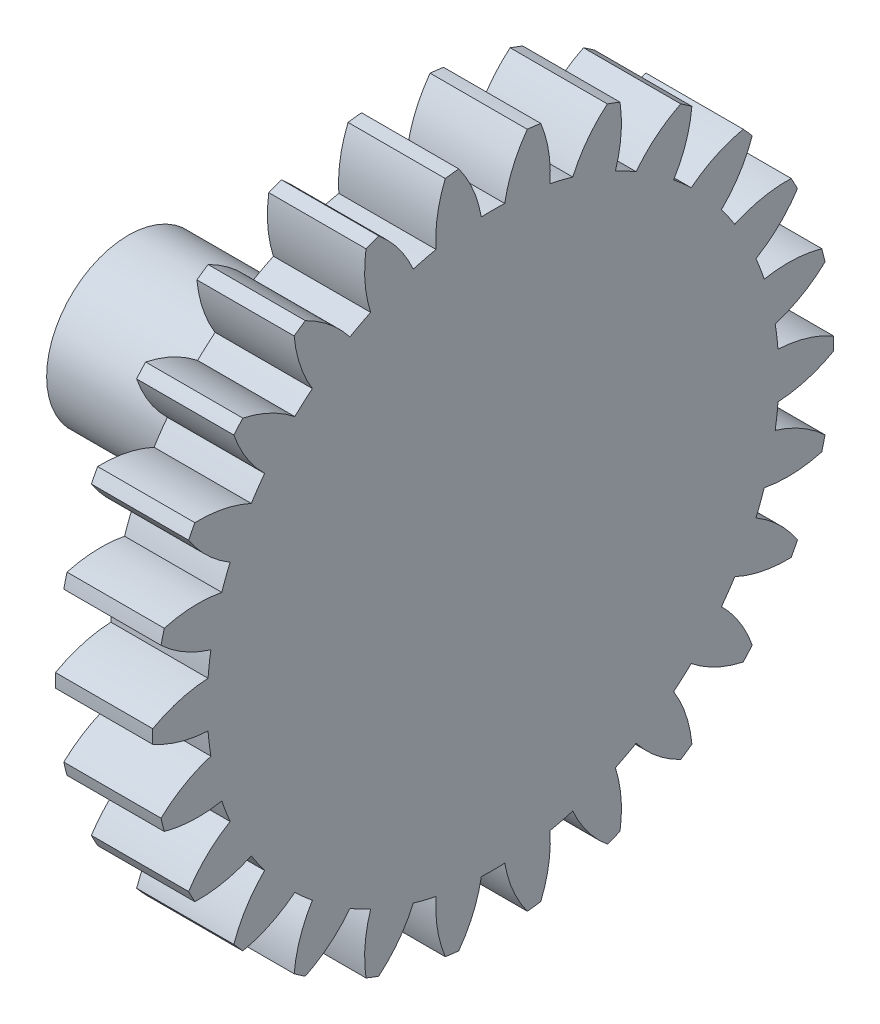
SolidWorks part; units mm, degrees
ref_plane "Plane1" through (0, 0, 0) normal (0, 0, 1) x (1, 0, 0)
ref_plane "Plane2" through (0, 0, 0) normal (0, 1, 0) x (1, 0, 0)
ref_plane "Plane3" through (0, 0, 0) normal (1, 0, 0) x (0, 0, -1)
sketch "HoldingSke" plane through (0, 0, 0) normal (0, 1, 0) x (1, 0, 0)
  line L0 (0, 0) -> (456.5874, -222.6925)
  line L1 (-15, 0) -> (100, 0) construction
  line L2 (0, 0) -> (-2.1039, 2.3779)
  line L3 (0, 0) -> (-11.863, 4.5341)
  line L4 (0, 0) -> (7.762, 3.7858)
  line L5 (0, 0) -> (-47.5972, -17.7524)
  line L6 (0, 0) -> (-4.2111, -2.8413)
  line L7 (-2.1039, 2.3779) -> (8.8308, 51.9871)
  line L8 (-76.2, 54.61) -> (-74.168, 54.61)
  line L9 (-71.009, 38.7566) -> (-53.1078, 45.2721)
  line L10 (-76.2, 71.12) -> (104.1128, 71.12)
  line L11 (0, 0) -> (-5.08, 0)
  line L12 (-76.2, 101.6) -> (-76.1492, 101.6)
  line L13 (24.9733, 27.94) -> (52.9518, 28.4284)
  line L14 (24.9733, 27.94) -> (25.0241, 27.9398)
  line L15 (24.9733, 27.94) -> (100.4021, 29.52)
  circle A0 centre (0, 0) radius 0.9995
  circle A1 centre (0, 0) radius 14.9352
  circle A2 centre (0, 0) radius 38.1
  circle A3 centre (0, 0) radius 0.9995
  dimension "MHD" = 29.8704
  dimension "Hub_dia" = 76.2
  dimension "Bore" = 1.999
  dimension "MBD" = 1.999
  dimension "Num_teeth" = 26
  dimension "Pitch" = 508
  dimension "Overall_len" = 50.8
  dimension "Show_teeth" = 26
  dimension "Thickness" = 5.08
  dimension "OAL" = 50.8001
  dimension "T_dim" = 2.032
  dimension "Ap" = 20
  dimension "H" = 19.05
  dimension "Pitch_radius" = 180.3128
  dimension "Width" = 5.08
  dimension "Backlash" = 0.0508
  dimension "Addendum_fac" = 1
  dimension "Dedendum_fac" = 1.2
  dimension "Clearance_fac" = 0.2
  dimension "Dedendum_add" = 0.0508
sketch "BasProSke" plane through (0, 0, 0) normal (0, 1, 0) x (1, 0, 0)
  line L0 (-10, 0) -> (60, 0) construction
  line L1 (0, 0) -> (0, 17.78)
  line L2 (0, 0) -> (5.08, 0)
  line L3 (5.08, 0) -> (5.08, 17.78)
  line L4 (5.08, 17.78) -> (0, 17.78)
  dimension "Thickness" = 5.08
  dimension "Diameter" = 35.56
revolve "Base-Revolve" add sketch "BasProSke" angle 360 about L0
sketch "TooCutSke" plane through (0, 0, 0) normal (1, 0, 0) x (0, 0, -1)
  line L1 (0, 0) -> (0, 107) construction
  line L2 (0, 0) -> (-1.0857, 16.4743) construction
  line L3 (0, 0) -> (-3.9741, 32.7296) construction
  line L4 (-1.0857, 16.4743) -> (-1.987, 16.3648) construction
  arc A0 (0.6122, 14.9226) -> (-0.6122, 14.9226) centre (0, 0) ccw
  arc A1 (1.8087, 17.7133) -> (-1.8087, 17.7133) centre (0, 0) ccw
  circle A2 centre (0, 0) radius 16.51 construction
  circle A3 centre (0, 0) radius 15.5143 construction
  arc A4 (-0.6122, 14.9226) -> (-1.8087, 17.7133) centre (-7.1175, 13.7853) ccw
  arc A5 (1.8087, 17.7133) -> (0.6122, 14.9226) centre (7.1175, 13.7853) ccw
  dimension "Root_dia" = 29.8704
  dimension "Overcut_dia" = 35.6108
  dimension "Pitch_dia" = 33.02
  dimension "Base_dia" = 31.0287
  dimension "Flank_rad" = 6.604
  dimension "Half_ang" = 6.923
  dimension "Half_CT" = 0.9079
extrude "ToothCut" cut sketch "TooCutSke" along normal through all
fillet "Breaks" [suppressed] radius 0.0254
fillet "RootFillets" [suppressed] radius 0.3048
pattern_circular "TeethCuts" count 26 every 13.846 about axis through (-10, 0, 0) along (1, 0, 0) of "ToothCut", "RootFillets", "Breaks"
sketch "HubNeaOneSke" plane through (0, 0, 0) normal (-1, 0, 0) x (0, 0, 1)
  circle A0 centre (0, 0) radius 14.9352
  dimension "Diameter" = 29.8704
extrude "HubNearOne" [suppressed] add sketch "HubNeaOneSke" along normal blind 45.7201
sketch "HubNeaBotSke" plane through (0, 0, 0) normal (-1, 0, 0) x (0, 0, 1)
  circle A0 centre (0, 0) radius 14.9352
  dimension "Diameter" = 29.8704
extrude "HubNearBoth" [suppressed] add sketch "HubNeaBotSke" along normal blind 22.86
ref_plane "FarPln" through (5.08, 0, 0) normal (1, 0, 0) x (0, 0, -1)
sketch "HubFarSke" plane through (5.08, 0, 0) normal (1, 0, 0) x (0, 0, -1)
  circle A0 centre (0, 0) radius 14.9352
  dimension "Diameter" = 29.8704
extrude "HubFar" [suppressed] add sketch "HubFarSke" along normal blind 22.86
sketch "BorSke" plane through (0, 0, 0) normal (1, 0, 0) x (0, 0, -1)
  circle A0 centre (0, 0) radius 0.9995
  dimension "Diameter" = 1.999
extrude "Bore" cut sketch "BorSke" along normal mid plane 101.6001
sketch "KeySke" plane through (0, 0, 0) normal (1, 0, 0) x (0, 0, -1)
  line L0 (-0.127, 0) -> (-0.127, 1.0325)
  line L1 (-0.127, 1.0325) -> (0.127, 1.0325)
  line L2 (0.127, 1.0325) -> (0.127, 0)
  line L3 (0, 0) -> (0, 34) construction
  line L4 (-0.127, 0) -> (0.127, 0)
  dimension "Offset" = 1.0325
  dimension "Width" = 0.254
extrude "Keyway" [suppressed] cut sketch "KeySke" along normal mid plane 101.6001
pattern_circular "Keyway2" [suppressed] count 2 every 90 about axis through (-10, 0, 0) along (1, 0, 0)
sketch "Sketch1" plane through (5.08, 0, 0) normal (1, 0, 0) x (0, 0, -1)
  circle A0 centre (0, 0) radius 0.9995
extrude "Boss-Extrude1" add sketch "Sketch1" against normal up to surface (5.08 mm away) up to face at (0, 0, -0.9995)
sketch "Sketch2" plane through (0, 0, 0) normal (-1, 0, 0) x (0, 0, 1)
  circle A0 centre (0, 0) radius 4.27
  dimension "D1" = 8.54
extrude "Boss-Extrude2" add sketch "Sketch2" along normal blind 13.97
sketch "Sketch3" plane through (-13.97, 0, 0) normal (-1, 0, 0) x (0, 0, 1)
  circle A0 centre (0, 0) radius 2.65
  dimension "D1" = 5.3
extrude "Cut-Extrude1" cut sketch "Sketch3" against normal blind 3.81
equation "' \"Pitch@HoldingSke\" = 4"
equation "' \"Num_teeth@HoldingSke\" = 12"
equation "' \"Ap@HoldingSke\" =  20"
equation "' \"Ap@HoldingSke\" = 20"
equation "' \"Width@HoldingSke\" = 0.5"
equation "' \"Hub_dia@HoldingSke\"= 1"
equation "' \"Hub_dia@HoldingSke\" = 1"
equation "' \"Overall_len@HoldingSke\" = 1.0"
equation "' \"Bore@HoldingSke\" = 0.75"
equation "' \"T_dim@HoldingSke\" = 0.85"
equation "' \"Width@KeySke\" = 0.25"
equation "' \"Show_teeth@HoldingSke\" = 13"
equation "' \"Backlash@HoldingSke\" = 0.009"
equation "' \"Addendum_fac@HoldingSke\" = 1.0"
equation "' \"Dedendum_fac@HoldingSke\" = 1.25"
equation "' \"Dedendum_add@HoldingSke\" = 0.00005"
equation "' \"Clearance_fac@HoldingSke\" = 0.25"
equation "' \"Pitch@HoldingSke\" = 0.5"
equation "' \"Num_teeth@HoldingSke\" = 23"
equation "' \"Show_teeth@HoldingSke\" = 23"
equation "' \"Backlash@HoldingSke\" = 0.0375"
equation "\"Overcut_dia@TooCutSke\" = (\"Num_teeth@HoldingSke\" + 2 * \"Addendum_fac@HoldingSke\") / \"Pitch@HoldingSke\" + 0.002"
equation "\"Pitch_dia@TooCutSke\" = \"Num_teeth@HoldingSke\" / \"Pitch@HoldingSke\""
equation "\"Base_dia@TooCutSke\" = \"Num_teeth@HoldingSke\" / \"Pitch@HoldingSke\" * cos((\"Ap@HoldingSke\"  * 3.14159265 / 180))"
equation "\"Root_dia@TooCutSke\" = (\"Num_teeth@HoldingSke\" + 2) / \"Pitch@HoldingSke\" - 2 * (\"Addendum_fac@HoldingSke\" + \"Dedendum_fac@HoldingSke\") / \"Pitch@HoldingSke\" - \"Dedendum_add@HoldingSke\" * 2"
equation "\"Half_ang@TooCutSke\" = 180 / \"Num_teeth@HoldingSke\""
equation "\"Half_CT@TooCutSke\" = \"Num_teeth@HoldingSke\" / \"Pitch@HoldingSke\" * sin((3.14159265 / 2 / \"Num_teeth@HoldingSke\")) / 2 - 7 * \"Backlash@HoldingSke\" / 4"
equation "\"Flank_rad@TooCutSke\" = \"Num_teeth@HoldingSke\" / \"Pitch@HoldingSke\" / 5"
equation "\"Radius@RootFillets\" = \"Clearance_fac@HoldingSke\" / \"Pitch@HoldingSke\" + \"Dedendum_add@HoldingSke\""
equation "\"Break_rad@Breaks\" = 0.02 / \"Pitch@HoldingSke\""
equation "\"Thickness@HoldingSke\" = \"Width@HoldingSke\""
equation "\"OAL@HoldingSke\" = \"Thickness@HoldingSke\""
equation "\"MHD@HoldingSke\" = (\"Num_teeth@HoldingSke\" + 2) / \"Pitch@HoldingSke\" - 2 * (\"Addendum_fac@HoldingSke\" + \"Dedendum_fac@HoldingSke\")  / \"Pitch@HoldingSke\" - \"Dedendum_add@HoldingSke\" * 2"
equation "\"MBD@HoldingSke\" = (\"Num_teeth@HoldingSke\" + 2) / \"Pitch@HoldingSke\" - 2 * (\"Addendum_fac@HoldingSke\" + \"Dedendum_fac@HoldingSke\")  / \"Pitch@HoldingSke\" - \"Dedendum_add@HoldingSke\" * 2 - 0.002"
equation "\"MHD@HoldingSke\" = ((sgn( \"MHD@HoldingSke\" - \"Hub_dia@HoldingSke\" )-1)*( \"MHD@HoldingSke\" - \"Hub_dia@HoldingSke\" ))/-2+ \"Hub_dia@HoldingSke\""
equation "\"MBD@HoldingSke\" = ((sgn( \"MBD@HoldingSke\" - \"Bore@HoldingSke\" )-1)*( \"MBD@HoldingSke\" - \"Bore@HoldingSke\" ))/-2+ \"Bore@HoldingSke\""
equation "\"OAL@HoldingSke\" = ((sgn( \"OAL@HoldingSke\" - \"Overall_len@HoldingSke\" )+1)*( \"OAL@HoldingSke\" - \"Overall_len@HoldingSke\" ))/2 + \"Overall_len@HoldingSke\" + 0.000002"
equation "\"Num_teeth@TeethCuts\" = int( \"Show_teeth@HoldingSke\" ) + 1"
equation "\"Num_teeth@TeethCuts\" = ((sgn( \"Num_teeth@TeethCuts\" - \"Num_teeth@HoldingSke\" )-1)*( \"Num_teeth@TeethCuts\" - \"Num_teeth@HoldingSke\" ))/-2+ \"Num_teeth@HoldingSke\""
equation "\"Num_teeth@TeethCuts\" = ((sgn( \"Num_teeth@TeethCuts\" - 2.0)+1)*( \"Num_teeth@TeethCuts\" - 2.0))/2 +2.0"
equation "\"Angle@TeethCuts\" = 360.0 / \"Num_teeth@HoldingSke\""
equation "\"Diameter@BasProSke\" = (\"Num_teeth@HoldingSke\" + 2 * \"Addendum_fac@HoldingSke\") / \"Pitch@HoldingSke\""
equation "\"Thickness@BasProSke\"  = \"Thickness@HoldingSke\""
equation "' \"Fillet_rad@BasProSke\" =  \"Thickness@HoldingSke\" * 0.05"
equation "' \"Fillet_rad@BasProSke\" = \"Thickness@HoldingSke\" * 0.05"
equation "\"MHD@HoldingSke\" = ((sgn( \"MHD@HoldingSke\" - \"Root_dia@TooCutSke\" )-1)*( \"MHD@HoldingSke\" - \"Root_dia@TooCutSke\" ))/-2+ \"Root_dia@TooCutSke\""
equation "\"Diameter@HubNeaOneSke\" = \"MHD@HoldingSke\""
equation "\"Length@HubNearOne\" = \"OAL@HoldingSke\" - \"Thickness@BasProSke\""
equation "\"Diameter@HubNeaBotSke\" = \"MHD@HoldingSke\""
equation "\"Length@HubNearBoth\" = ( \"OAL@HoldingSke\" - \"Thickness@BasProSke\" ) / 2.0"
equation "\"Thickness@FarPln\" = \"Thickness@BasProSke\""
equation "\"Diameter@HubFarSke\" = \"MHD@HoldingSke\""
equation "\"Length@HubFar\" = ( \"OAL@HoldingSke\" - \"Thickness@BasProSke\" ) / 2.0"
equation "\"Diameter@BorSke\" = \"MBD@HoldingSke\""
equation "\"D1@Bore\" = \"OAL@HoldingSke\" * 2.0"
equation "\"D1@Keyway\" = \"OAL@HoldingSke\" * 2.0"
equation "\"Offset@KeySke\" = \"T_dim@HoldingSke\" - \"MBD@HoldingSke\" / 2.0"
